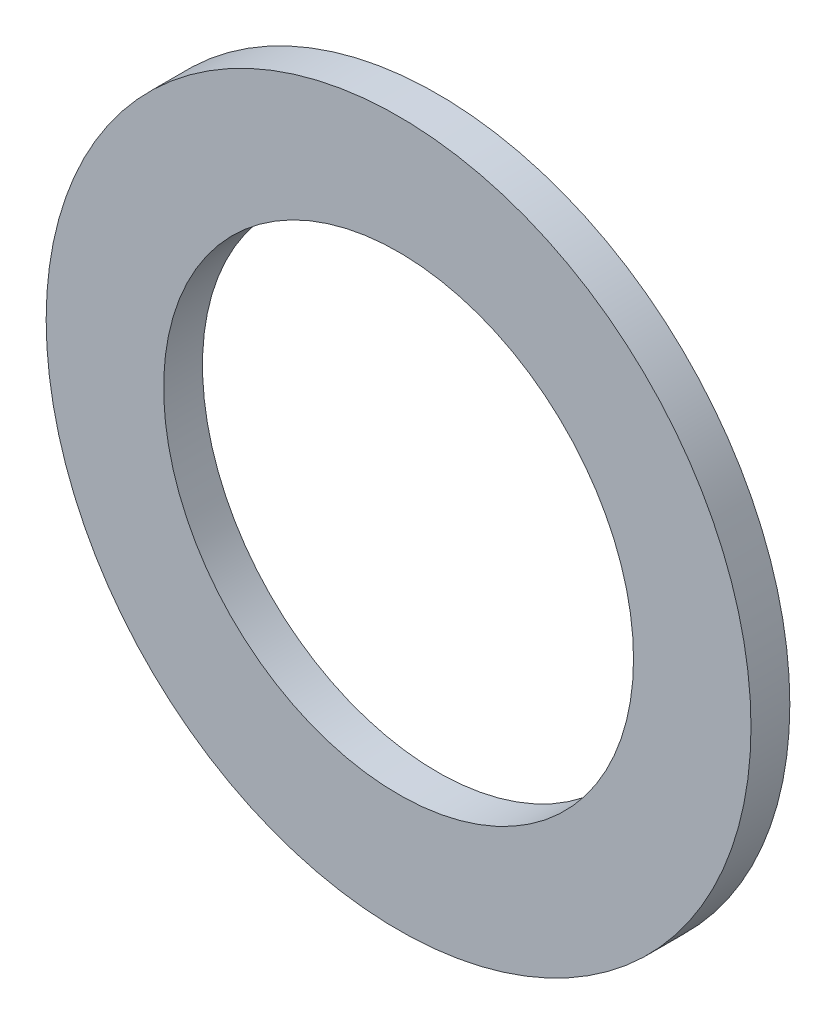
SolidWorks part; units mm, degrees
material "Plain Carbon Steel"
ref_plane "Front Plane" through (0, 0, 0) normal (0, 0, 1) x (1, 0, 0)
ref_plane "Top Plane" through (0, 0, 0) normal (0, 1, 0) x (1, 0, 0)
ref_plane "Right Plane" through (0, 0, 0) normal (1, 0, 0) x (0, 0, -1)
sketch "Sketch1" plane through (0, 0, 0) normal (0, 0, 1) x (1, 0, 0)
  circle A0 centre (0, 0) radius 9.525
  circle A1 centre (0, 0) radius 14.2875
  dimension "D1" = 19.05
  dimension "D2" = 28.575
extrude "Boss-Extrude1" add sketch "Sketch1" along normal blind 1.5748
